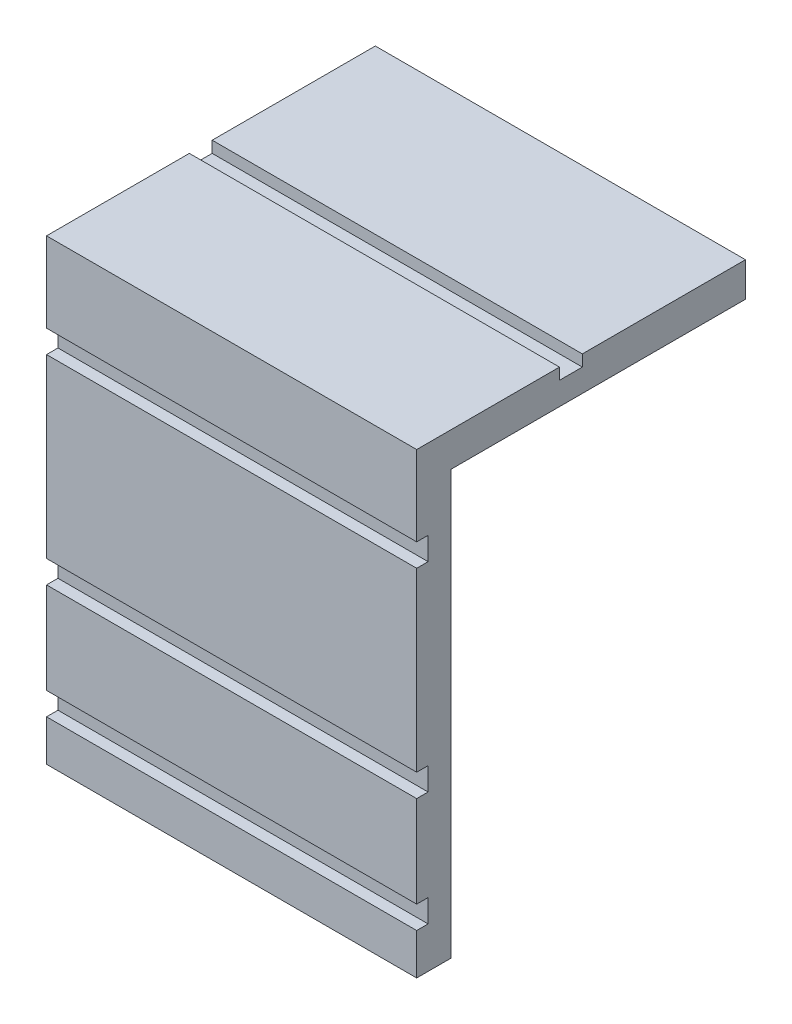
SolidWorks part; units mm, degrees
ref_plane "Front Plane" through (0, 0, 0) normal (0, 0, 1) x (1, 0, 0)
ref_plane "Top Plane" through (0, 0, 0) normal (0, 1, 0) x (1, 0, 0)
ref_plane "Right Plane" through (0, 0, 0) normal (1, 0, 0) x (0, 0, -1)
sketch "Sketch1" plane through (0, 0, 0) normal (1, 0, 0) x (0, 0, -1)
  line L0 (0, 0) -> (0, 1.8)
  line L1 (0, 1.8) -> (0.5, 1.8)
  line L2 (0.5, 1.8) -> (0.5, 2.8)
  line L3 (0.5, 2.8) -> (0, 2.8)
  line L4 (0, 2.8) -> (0, 6.8)
  line L5 (0, 7.8) -> (0.5, 7.8)
  line L6 (0.5, 7.8) -> (0.5, 6.8)
  line L7 (0.5, 6.8) -> (0, 6.8)
  line L8 (0, 7.8) -> (0, 15.53)
  line L9 (0, 16.53) -> (0.5, 16.53)
  line L10 (0.5, 16.53) -> (0.5, 15.53)
  line L11 (0.5, 15.53) -> (0, 15.53)
  line L12 (0, 16.53) -> (0, 20.03)
  line L13 (0, 20.03) -> (6.25, 20.03)
  line L14 (6.25, 20.03) -> (6.25, 19.53)
  line L15 (6.25, 19.53) -> (7.25, 19.53)
  line L16 (7.25, 19.53) -> (7.25, 20.03)
  line L17 (7.25, 20.03) -> (14.39, 20.03)
  line L18 (14.39, 20.03) -> (14.39, 18.53)
  line L19 (14.39, 18.53) -> (1.5, 18.53)
  line L20 (1.5, 18.53) -> (1.5, 0)
  line L21 (1.5, 0) -> (0, 0)
  dimension "D1" = 1
  dimension "D2" = 20.03
  dimension "D3" = 1.5
  dimension "D4" = 1.5
  dimension "D5" = 1
  dimension "D6" = 0.5
  dimension "D7" = 14.39
  dimension "D8" = 6.25
  dimension "D9" = 3.5
  dimension "D10" = 0.5
  dimension "D11" = 1
  dimension "D12" = 0.5
  dimension "D13" = 1.8
  dimension "D14" = 5
  dimension "D15" = 1
  dimension "D16" = 0.5
extrude "Boss-Extrude1" add sketch "Sketch1" along normal blind 16.2
